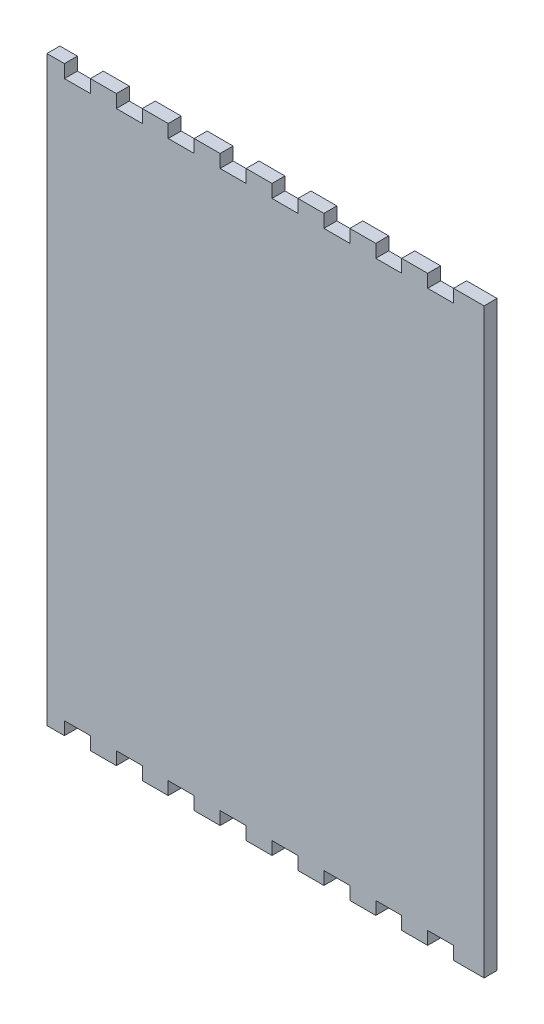
SolidWorks part; units mm, degrees
ref_plane "Front Plane" through (0, 0, 0) normal (0, 0, 1) x (1, 0, 0)
ref_plane "Top Plane" through (0, 0, 0) normal (0, 1, 0) x (1, 0, 0)
ref_plane "Right Plane" through (0, 0, 0) normal (1, 0, 0) x (0, 0, -1)
sketch "Model" plane through (0, 0, 0) normal (0, 0, 1) x (1, 0, 0)
  line L657 (960.9734, 23.2006) -> (968.69, 23.2006)
  line L658 (968.69, 23.2006) -> (968.69, 28.9154)
  line L659 (968.69, 28.9154) -> (980.12, 28.9154)
  line L660 (980.12, 28.9154) -> (980.12, 23.2006)
  line L661 (980.12, 23.2006) -> (991.55, 23.2006)
  line L662 (991.55, 23.2006) -> (991.55, 28.9154)
  line L663 (991.55, 28.9154) -> (1002.98, 28.9154)
  line L664 (1002.98, 28.9154) -> (1002.98, 23.2006)
  line L665 (1002.98, 23.2006) -> (1014.41, 23.2006)
  line L666 (1014.41, 23.2006) -> (1014.41, 28.9154)
  line L667 (1014.41, 28.9154) -> (1025.84, 28.9154)
  line L668 (1025.84, 28.9154) -> (1025.84, 23.2006)
  line L669 (1025.84, 23.2006) -> (1037.27, 23.2006)
  line L670 (1037.27, 23.2006) -> (1037.27, 28.9154)
  line L671 (1037.27, 28.9154) -> (1048.7, 28.9154)
  line L672 (1048.7, 28.9154) -> (1048.7, 23.2006)
  line L673 (1048.7, 23.2006) -> (1060.13, 23.2006)
  line L674 (1060.13, 23.2006) -> (1060.13, 28.9154)
  line L675 (1060.13, 28.9154) -> (1071.56, 28.9154)
  line L676 (1071.56, 28.9154) -> (1071.56, 23.2006)
  line L677 (1071.56, 23.2006) -> (1082.99, 23.2006)
  line L678 (1082.99, 23.2006) -> (1082.99, 28.9154)
  line L679 (1082.99, 28.9154) -> (1094.42, 28.9154)
  line L680 (1094.42, 28.9154) -> (1094.42, 23.2006)
  line L681 (1094.42, 23.2006) -> (1105.85, 23.2006)
  line L682 (1105.85, 23.2006) -> (1105.85, 28.9154)
  line L683 (1105.85, 28.9154) -> (1117.28, 28.9154)
  line L684 (1117.28, 28.9154) -> (1117.28, 23.2006)
  line L685 (1117.28, 23.2006) -> (1128.71, 23.2006)
  line L686 (1128.71, 23.2006) -> (1128.71, 28.9154)
  line L687 (1128.71, 28.9154) -> (1140.14, 28.9154)
  line L688 (1140.14, 28.9154) -> (1140.14, 23.2006)
  line L689 (1140.14, 23.2006) -> (1153.5715, 23.2006)
  line L690 (1153.5715, 23.2006) -> (1153.5715, 279.6311)
  line L691 (1153.5715, 279.6311) -> (1140.14, 279.6311)
  line L692 (1140.14, 279.6311) -> (1140.14, 273.9161)
  line L693 (1140.14, 273.9161) -> (1128.71, 273.9161)
  line L694 (1128.71, 273.9161) -> (1128.71, 279.6311)
  line L695 (1128.71, 279.6311) -> (1117.28, 279.6311)
  line L696 (1117.28, 279.6311) -> (1117.28, 273.9161)
  line L697 (1117.28, 273.9161) -> (1105.85, 273.9161)
  line L698 (1105.85, 273.9161) -> (1105.85, 279.6311)
  line L699 (1105.85, 279.6311) -> (1094.42, 279.6311)
  line L700 (1094.42, 279.6311) -> (1094.42, 273.9161)
  line L701 (1094.42, 273.9161) -> (1082.99, 273.9161)
  line L702 (1082.99, 273.9161) -> (1082.99, 279.6311)
  line L703 (1082.99, 279.6311) -> (1071.56, 279.6311)
  line L704 (1071.56, 279.6311) -> (1071.56, 273.9161)
  line L705 (1071.56, 273.9161) -> (1060.13, 273.9161)
  line L706 (1060.13, 273.9161) -> (1060.13, 279.6311)
  line L707 (1060.13, 279.6311) -> (1048.7, 279.6311)
  line L708 (1048.7, 279.6311) -> (1048.7, 273.9161)
  line L709 (1048.7, 273.9161) -> (1037.27, 273.9161)
  line L710 (1037.27, 273.9161) -> (1037.27, 279.6311)
  line L711 (1037.27, 279.6311) -> (1025.84, 279.6311)
  line L712 (1025.84, 279.6311) -> (1025.84, 273.9161)
  line L713 (1025.84, 273.9161) -> (1014.41, 273.9161)
  line L714 (1014.41, 273.9161) -> (1014.41, 279.6311)
  line L715 (1014.41, 279.6311) -> (1002.98, 279.6311)
  line L716 (1002.98, 279.6311) -> (1002.98, 273.9161)
  line L717 (1002.98, 273.9161) -> (991.55, 273.9161)
  line L718 (991.55, 273.9161) -> (991.55, 279.6311)
  line L719 (991.55, 279.6311) -> (980.12, 279.6311)
  line L720 (980.12, 279.6311) -> (980.12, 273.9161)
  line L721 (980.12, 273.9161) -> (968.69, 273.9161)
  line L722 (968.69, 273.9161) -> (968.69, 279.6311)
  line L723 (968.69, 279.6311) -> (960.9734, 279.6311)
  line L724 (960.9734, 279.6311) -> (960.9734, 23.2006)
  text T12 "T" font "SWTXT" height 4
  text T13 "op" font "SWTXT" height 4
extrude "Boss-Extrude1" add sketch "Model" along normal blind 5.715 contours L723 L724 L657 L658 L659 L660 L661 L662 L663 L664 L665 L666 L667 L668 L669 L670 L671 L672 L673 L674 L675 L676 L677 L678 L679 L680 L681 L682 L683 L684 L685 L686 L687 L688 L689 L690 L691 L692 L693 L694 L695 L696 L697 L698 L699 L700 L701 L702 L703 L704 L705
